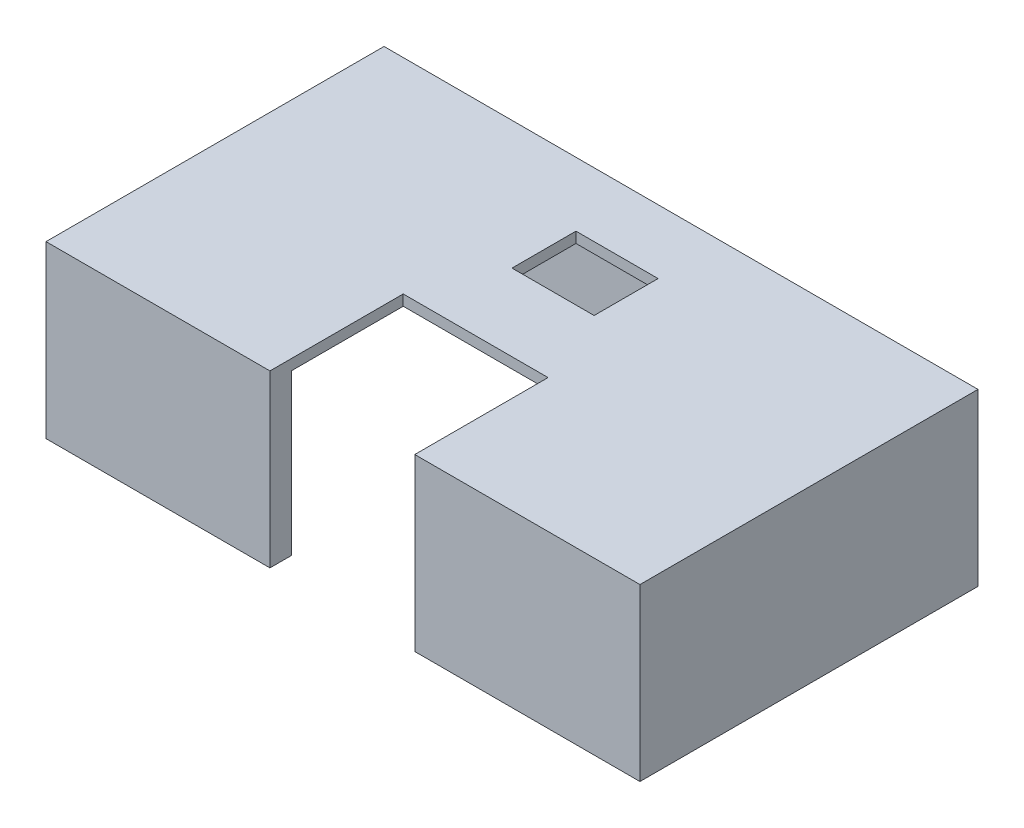
SolidWorks part; units mm, degrees
ref_plane "Front Plane" through (0, 0, 0) normal (0, 0, 1) x (1, 0, 0)
ref_plane "Top Plane" through (0, 0, 0) normal (0, 1, 0) x (1, 0, 0)
ref_plane "Right Plane" through (0, 0, 0) normal (1, 0, 0) x (0, 0, -1)
sketch "Sketch1" plane through (0, 0, 0) normal (0, 1, 0) x (1, 0, 0)
  line L1 (0, 0) -> (55.7, 0)
  line L2 (0, 0) -> (0, 31.7)
  line L3 (0, 31.7) -> (55.7, 31.7)
  line L4 (55.7, 0) -> (55.7, 31.7)
  dimension "D1" = 55.7
  dimension "D2" = 31.7
extrude "Boss-Extrude1" add sketch "Sketch1" along normal blind 16
sketch "Sketch3" plane through (0, 0, 0) normal (0, -1, 0) x (1, 0, 0)
  line L0 (0, -31.7) -> (0, 0) construction
  line L1 (2, -2) -> (53.7, -2)
  line L2 (2, -2) -> (2, -29.7)
  line L3 (2, -29.7) -> (53.7, -29.7)
  line L4 (53.7, -2) -> (53.7, -29.7)
  line L5 (0, 0) -> (55.7, 0) construction
  line L6 (55.7, -31.7) -> (0, -31.7) construction
  line L8 (55.7, 0) -> (55.7, -31.7) construction
  dimension "D1" = 2
  dimension "D2" = 2
  dimension "D3" = 2
  dimension "D4" = 2
extrude "Cut-Extrude2" cut sketch "Sketch3" against normal blind 15
sketch "Sketch4" plane through (0, 15, 0) normal (0, -1, 0) x (1, 0, 0)
  line L9 (21, -12.5) -> (34.5816, -12.5)
  line L10 (21, -12.5) -> (21, 0.8168)
  line L11 (21, 0.8168) -> (34.5816, 0.8168)
  line L12 (34.5816, -12.5) -> (34.5816, 0.8168)
extrude "Cut-Extrude3" cut sketch "Sketch4" along normal through all from offset 5 offset against normal yes
sketch "Sketch5" plane through (0, 15, 0) normal (0, -1, 0) x (1, 0, 0)
  line L0 (26.0165, -29.7) -> (26.0165, -19.7) construction
  line L1 (2, -29.7) -> (53.7, -29.7) construction
  line L2 (53.7, -29.7) -> (53.7, -2) construction
  line L3 (24, -25.7) -> (31.7, -25.7)
  line L4 (24, -25.7) -> (24, -19.7)
  line L5 (24, -19.7) -> (31.7, -19.7)
  line L6 (31.7, -25.7) -> (31.7, -19.7)
  line L7 (2, -2) -> (2, -29.7) construction
  line L8 (2, -29.7) -> (53.7, -29.7) construction
  point P8 (35.0088, -24.5242)
  point P11 (24, -22.7)
  dimension "D1" = 10
  dimension "D2" = 22
  dimension "D3" = 22
  dimension "D4" = 6
  dimension "D5" = 10
extrude "Cut-Extrude4" cut sketch "Sketch5" against normal blind 10
sketch "Sketch7" plane through (0, 0, 0) normal (-1, 0, 0) x (0, 0, 1)
  line L2 (-22.7, 14.2831) -> (-9, 14.2831)
  line L3 (-22.7, 14.2831) -> (-22.7, -0.7132)
  line L4 (-22.7, -0.7132) -> (-9, -0.7132)
  line L5 (-9, 14.2831) -> (-9, -0.7132)
  line L6 (-31.7, 16) -> (-31.7, 0) construction
  line L7 (0, 16) -> (0, 0) construction
  point P0 (-22.7, -0.7132)
  point P10 (0, 0)
  dimension "D3" = 9
  dimension "D4" = 9
extrude "Cut-Extrude5" cut sketch "Sketch7" against normal blind 10
